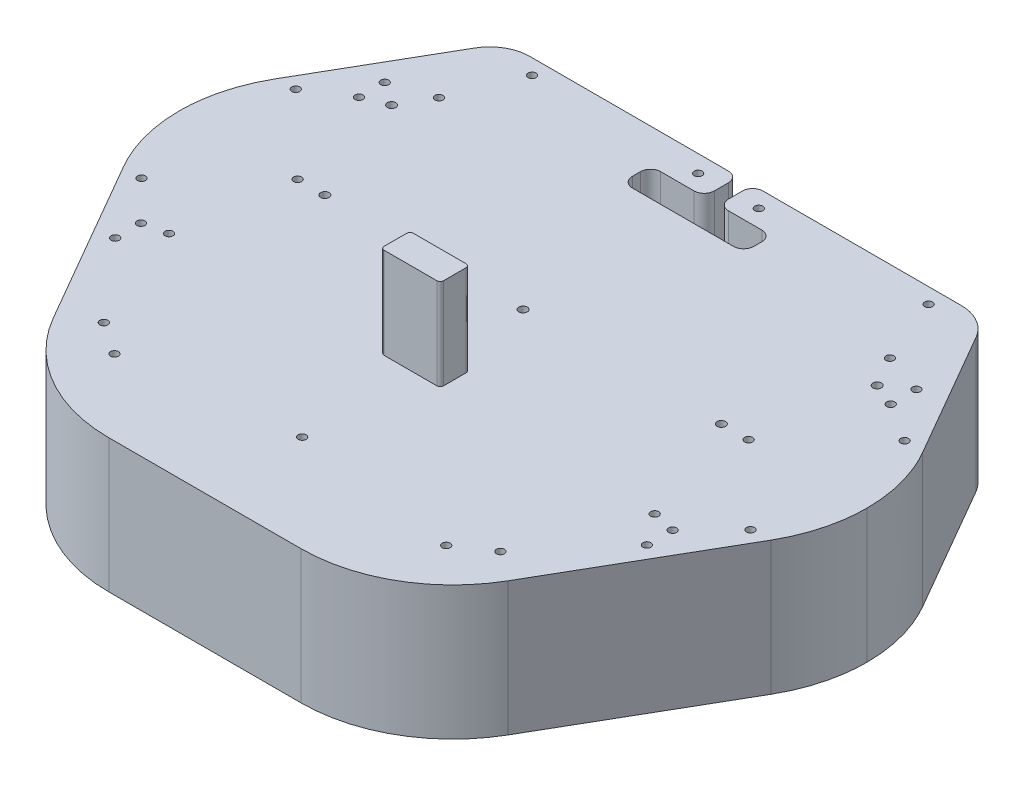
SolidWorks part; units mm, degrees
ref_plane "Front Plane" through (0, 0, 0) normal (0, 0, 1) x (1, 0, 0)
ref_plane "Top Plane" through (0, 0, 0) normal (0, 1, 0) x (1, 0, 0)
ref_plane "Right Plane" through (0, 0, 0) normal (1, 0, 0) x (0, 0, -1)
ref_plane "Plane1" through (0, 6, 0) normal (0, 1, 0) x (1, 0, 0)
sketch "Sketch1" plane through (0, 6, 0) normal (0, 1, 0) x (1, 0, 0)
  line L0 (118.094, 110) -> (-118.094, 110)
  line L1 (-118.094, 110) -> (-159.9519, 37.5)
  line L2 (-159.9519, -37.5) -> (-90.8013, -157.2724)
  line L3 (-90.8013, -157.2724) -> (90.8013, -157.2724)
  line L4 (90.8013, -157.2724) -> (159.9519, -37.5)
  line L5 (159.9519, 37.5) -> (118.094, 110)
  spline S0 degree 3 poles (-159.9519, 37.5) (-162.0898, 33.7968) (-165.8426, 25.7861) (-169.2445, 13.0899) (-169.9999, 4.2761) (-170, 0) knots 5.759587 5.759587 5.759587 5.759587 5.930629 6.112143 6.283185 6.283185 6.283185 6.283185
  spline S1 degree 3 poles (-170, 0) (-169.9999, -4.2761) (-169.2445, -13.0899) (-165.8426, -25.7861) (-162.0898, -33.7968) (-159.9519, -37.5) knots 0 0 0 0 0.171042 0.352557 0.523599 0.523599 0.523599 0.523599
  spline S2 degree 3 poles (159.9519, -37.5) (162.0898, -33.7968) (165.8426, -25.7861) (169.2445, -13.0899) (169.9999, -4.2761) (170, 0) knots 2.617994 2.617994 2.617994 2.617994 2.789036 2.97055 3.141593 3.141593 3.141593 3.141593
  spline S3 degree 3 poles (170, 0) (169.9999, 4.276) (169.2445, 13.0899) (165.8426, 25.7861) (162.0898, 33.7968) (159.9519, 37.5) knots 3.141593 3.141593 3.141593 3.141593 3.312635 3.494149 3.665191 3.665191 3.665191 3.665191
extrude "Boss-Extrude1" add sketch "Sketch1" against normal up to surface (66 mm away)
sketch "Sketch2" plane through (0, -60, 0) normal (0, -1, 0) x (1, 0, 0)
  line L0 (3.5, -110) -> (3.5, -93)
  line L1 (3.5, -93) -> (30, -93)
  line L2 (30, -93) -> (30, -79)
  line L3 (30, -79) -> (-30, -79)
  line L4 (-30, -79) -> (-30, -93)
  line L5 (-30, -93) -> (-3.5, -93)
  line L6 (-3.5, -93) -> (-3.5, -110)
  line L7 (-3.5, -110) -> (3.5, -110)
extrude "Cut-Extrude1" cut sketch "Sketch2" against normal through all
hole_wizard "M3.5 Clearance Hole1" positions "Sketch4" profile "Sketch3" hole size "M3.5" standard "ANSI Metric"
sketch "Sketch4" plane through (0, -60, 0) normal (0, -1, 0) x (-1, 0, 0)
  point P0 (0, -0.0015)
  point P1 (-97.9932, 0.0015)
  point P2 (97.9932, 0.0015)
  point P3 (120, 55.0015)
  point P4 (-120, 55.0015)
sketch "Sketch3" plane through (0, -60, 0.0015) normal (1, 0, 0) x (0, 0, -1)
  line L0 (0, 0) -> (0, 66.0001)
  line L1 (0, 66.0001) -> (2.0999, 66.0001)
  line L2 (2.0999, 66.0001) -> (2.0999, 0)
  line L5 (2.0999, 0) -> (0, 0)
  line L11 (0, -6.35) -> (0, 107.95) construction
  dimension "Thru Hole Dia." = 4.1998
  dimension "Thru Hole Depth" = 66.0001
hole_wizard "M3.5 Clearance Hole2" positions "Sketch6" profile "Sketch5" hole size "M3.5" standard "ANSI Metric"
sketch "Sketch6" plane through (0, -60, 0) normal (0, -1, 0) x (-1, 0, 0)
  point P0 (98, 102.4382)
  point P1 (0, -109.22)
  point P2 (98, -109.22)
  point P3 (-98, -109.22)
  point P4 (111.4552, 69.85)
  point P5 (111.4552, 0)
  point P6 (-111.4552, 69.85)
  point P7 (-111.4552, 0)
  point P8 (-120, -55)
  point P9 (120, -55)
  point P10 (131.4, 50.3)
  point P11 (-131.4, 50.3)
  point P12 (131.4, -70.2)
  point P13 (-131.4, -70.2)
  point P14 (131.4, 63)
  point P15 (-131.4, 63)
  point P16 (131.4, -57.5)
  point P17 (-131.4, -57.5)
  point P18 (15, 101.5)
  point P19 (-98, 102.4382)
  point P20 (-15, 101.5)
  point P21 (150.47, 38.1)
  point P22 (150.47, -38.1)
  point P23 (-150.47, 38.1)
  point P24 (-150.47, -38.1)
  point P25 (-82, -120)
  point P26 (82, -120)
sketch "Sketch5" plane through (-98, -60, -102.4382) normal (1, 0, 0) x (0, 0, -1)
  line L0 (0, 0) -> (0, 66.0001)
  line L1 (0, 66.0001) -> (1.9748, 66.0001)
  line L2 (1.9748, 66.0001) -> (1.9748, 0)
  line L5 (1.9748, 0) -> (0, 0)
  line L11 (0, -6.35) -> (0, 107.95) construction
  dimension "Thru Hole Dia." = 3.9496
  dimension "Thru Hole Depth" = 66.0001
fillet "Fillet1" radius 5.0247 8 edges at (-30, -27, -79) (30, -27, -79) (-30, -27, -93) (-3.5, -27, -93) (30, -27, -93) (3.5, -27, -93)
fillet "Fillet2" radius 19.9245 2 edges at (118.094, -27, -110) (-118.094, -27, -110)
fillet "Fillet3" radius 74.9585 2 edges at (-90.8013, -27, 157.2724) (90.8013, -27, 157.2724)
sketch "Sketch7" plane through (0, 6, 0) normal (0, 1, 0) x (1, 0, 0)
  line L0 (-16.3908, -41.2673) -> (-16.4109, -52.2655)
  line L1 (-14.6904, -53.9915) -> (11.3096, -53.9915)
  line L3 (13.0302, -52.2655) -> (13.0101, -41.2673)
  line L4 (11.3096, -39.5022) -> (-14.6904, -39.5022)
  arc A0 (13.0101, -41.2673) -> (11.3096, -39.5022) centre (11.2403, -41.2706) ccw
  arc A1 (-14.6904, -39.5022) -> (-16.3908, -41.2673) centre (-14.6904, -41.2038) ccw
  arc A2 (-16.4109, -52.2655) -> (-14.6904, -53.9915) centre (-14.6904, -52.2709) ccw
  arc A3 (11.3096, -53.9915) -> (13.0302, -52.2655) centre (11.3096, -52.2709) ccw
extrude "Boss-Extrude2" add sketch "Sketch7" along normal up to surface (45 mm away)
